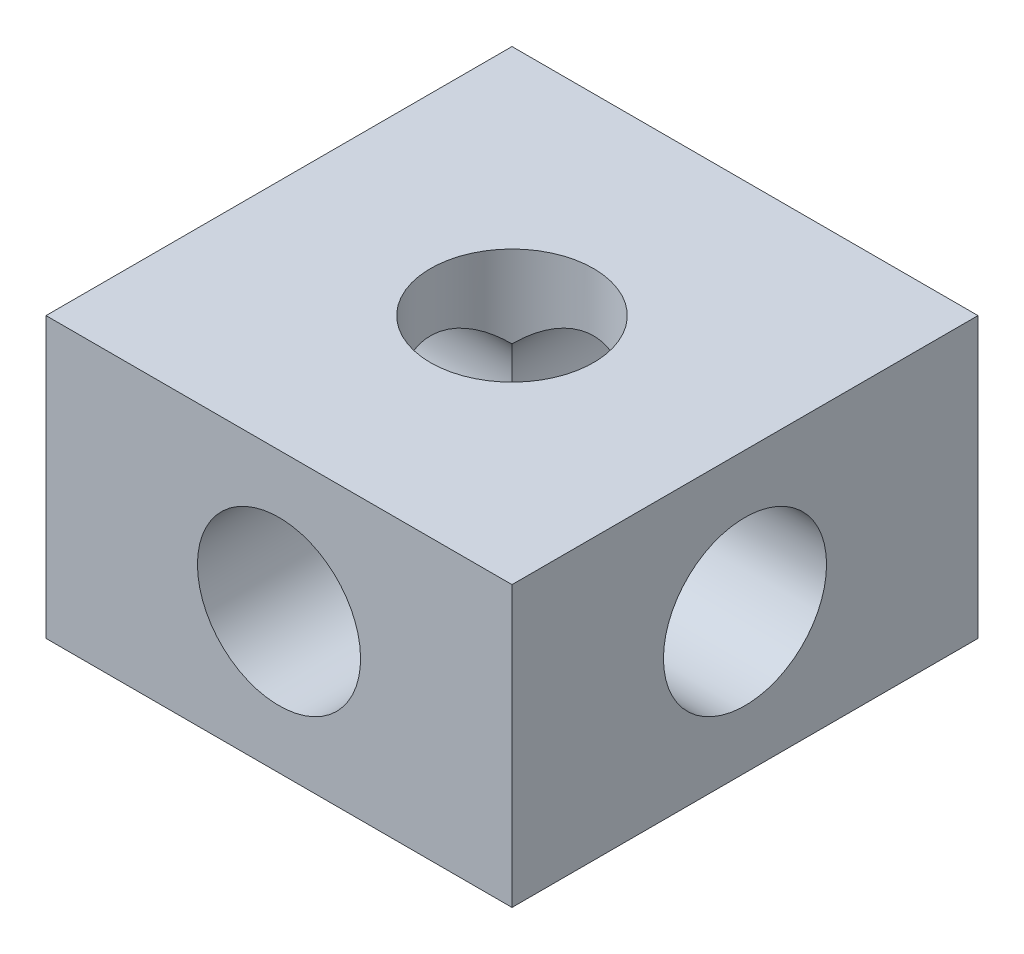
SolidWorks part; units mm, degrees
ref_plane "前视基准面" through (0, 0, 0) normal (0, 0, 1) x (1, 0, 0)
ref_plane "上视基准面" through (0, 0, 0) normal (0, 1, 0) x (1, 0, 0)
ref_plane "右视基准面" through (0, 0, 0) normal (1, 0, 0) x (0, 0, -1)
sketch "草图1" plane through (0, 0, 0) normal (0, 1, 0) x (1, 0, 0)
  line L1 (-5, 5) -> (5, 5)
  line L2 (-5, 5) -> (-5, -5)
  line L3 (-5, -5) -> (5, -5)
  line L4 (5, 5) -> (5, -5)
  line L5 (-5, 5) -> (5, -5) construction
  line L6 (-5, -5) -> (5, 5) construction
  circle A0 centre (0, 0) radius 1.75
  point P0 (0, 0)
  dimension "D2" = 3.5
  dimension "D1" = 10
extrude "凸台-拉伸1" add sketch "草图1" along normal mid plane 6
sketch "草图3" plane through (0, 0, 0) normal (0, 0, 1) x (1, 0, 0)
  circle A0 centre (0, 0) radius 1.75
  dimension "D1" = 3.5
extrude "切除-拉伸1" cut sketch "草图3" against normal mid plane 17
sketch "草图4" plane through (0, 0, 0) normal (1, 0, 0) x (0, 0, -1)
  circle A0 centre (0, 0) radius 1.75
  dimension "D1" = 3.5
extrude "切除-拉伸2" cut sketch "草图4" against normal mid plane 17
